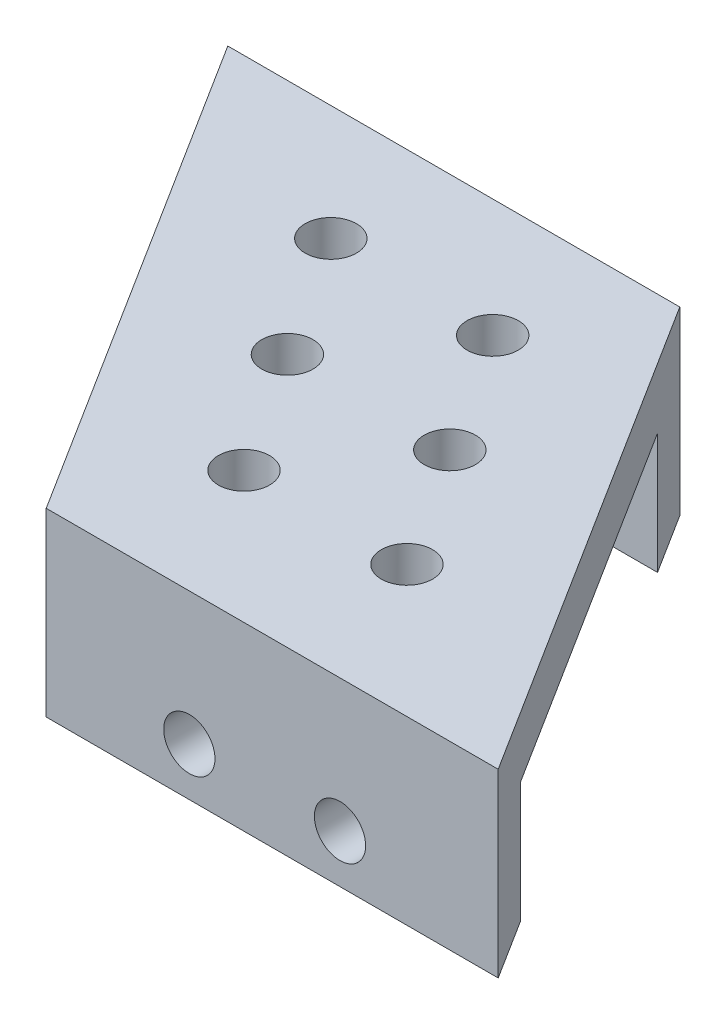
SolidWorks part; units mm, degrees
ref_plane "Piano frontale" through (0, 0, 0) normal (0, 0, 1) x (1, 0, 0)
ref_plane "Piano superiore" through (0, 0, 0) normal (0, 1, 0) x (1, 0, 0)
ref_plane "Piano destro" through (0, 0, 0) normal (1, 0, 0) x (0, 0, -1)
sketch "Schizzo1" plane through (0, 0, 0) normal (0, 1, 0) x (1, 0, 0)
  line L12 (1.586, 7.0646) -> (22.1333, -25.5354)
  line L13 (22.1333, -25.5354) -> (-7.8667, -25.5354)
  line L24 (-28.414, 7.0646) -> (1.586, 7.0646)
  line L26 (-7.8667, -25.5354) -> (-28.414, 7.0646)
  dimension "D1" = 32.6
  dimension "D2" = 30
  dimension "D3" = 5.1086
extrude "Estrusione-Estrusione1" add sketch "Schizzo1" along normal blind 4
sketch "Schizzo4" plane through (0, 0, 0) normal (0, -1, 0) x (1, 0, 0)
  line L0 (-28.414, -7.0646) -> (-25.8929, -3.0646)
  line L1 (-28.414, -7.0646) -> (-7.8667, 25.5354) construction
  line L2 (-25.8929, -3.0646) -> (4.1071, -3.0646)
  line L3 (22.1333, 25.5354) -> (1.586, -7.0646) construction
  line L4 (4.1071, -3.0646) -> (1.586, -7.0646)
  line L5 (1.586, -7.0646) -> (-28.414, -7.0646)
  line L6 (22.1333, 25.5354) -> (-7.8667, 25.5354)
  line L7 (-7.8667, 25.5354) -> (-10.3879, 21.5354)
  line L8 (-10.3879, 21.5354) -> (19.6121, 21.5354)
  line L9 (19.6121, 21.5354) -> (22.1333, 25.5354)
  dimension "D1" = 4
  dimension "D2" = 4
extrude "Estrusione-Estrusione2" add sketch "Schizzo4" along normal blind 8
sketch "Schizzo7" plane through (0, 4, 0) normal (0, 1, 0) x (1, 0, 0)
  line L0 (7.3293, -16.7878) -> (-3.4876, -16.7878)
  line L1 (-3.4876, -16.7878) -> (-13.9358, -0.5762)
  line L2 (-13.9358, -0.5762) -> (-2.9886, -0.7783)
  line L3 (-2.9886, -0.7783) -> (7.3293, -16.7878)
  line L5 (-28.414, 7.0646) -> (-7.8667, -25.5354) construction
  line L6 (1.586, 7.0646) -> (-28.414, 7.0646) construction
  circle A0 centre (7.3293, -16.7878) radius 1.7
  circle A3 centre (-3.4876, -16.7878) radius 1.7
  circle A4 centre (-8.7117, -8.682) radius 1.7
  circle A5 centre (-13.9358, -0.5762) radius 1.7
  circle A6 centre (-2.9886, -0.7783) radius 1.7
  circle A7 centre (2.1703, -8.7831) radius 1.7
  dimension "D1" = 3.4
  dimension "D2" = 3.4
  dimension "D3" = 3.4
  dimension "D4" = 3.4
  dimension "D5" = 3.4
  dimension "D6" = 3.4
  dimension "D7" = 0.579
  dimension "D8" = 1.058
extrude "Taglio-Estrusione4" cut sketch "Schizzo7" against normal through all contours A3 | A0 | A7 | A6 | A5 | A4
sketch "Schizzo10" plane through (0, 0, 25.5354) normal (0, 0, 1) x (1, 0, 0)
  line L0 (-7.8667, 4) -> (-7.8667, -8) construction
  line L1 (22.1333, 4) -> (22.1333, -8) construction
  line L2 (22.1333, -8) -> (-7.8667, -8) construction
  circle A0 centre (1.6333, -4.8) radius 1.7
  circle A1 centre (11.6333, -4.8) radius 1.7
  dimension "D1" = 3.4
  dimension "D2" = 3.4
  dimension "D4" = 10.5
  dimension "D6" = 3.2
  dimension "D3" = 9.5
  dimension "D5" = 3.2
extrude "Taglio-Estrusione5" cut sketch "Schizzo10" against normal blind 10
sketch "Schizzo11" plane through (0, 0, -7.0646) normal (0, 0, -1) x (-1, 0, 0)
  line L0 (28.414, -8) -> (-1.586, -8) construction
  line L1 (28.414, 4) -> (28.414, -8) construction
  line L2 (-1.586, 4) -> (-1.586, -8) construction
  circle A0 centre (9.414, -4.8) radius 1.7
  circle A1 centre (19.414, -4.8) radius 1.7
  dimension "D1" = 3.4
  dimension "D2" = 3.4
  dimension "D6" = 11
  dimension "D3" = 3.2
  dimension "D4" = 3.2
  dimension "D5" = 9
extrude "Taglio-Estrusione6" cut sketch "Schizzo11" against normal blind 10
